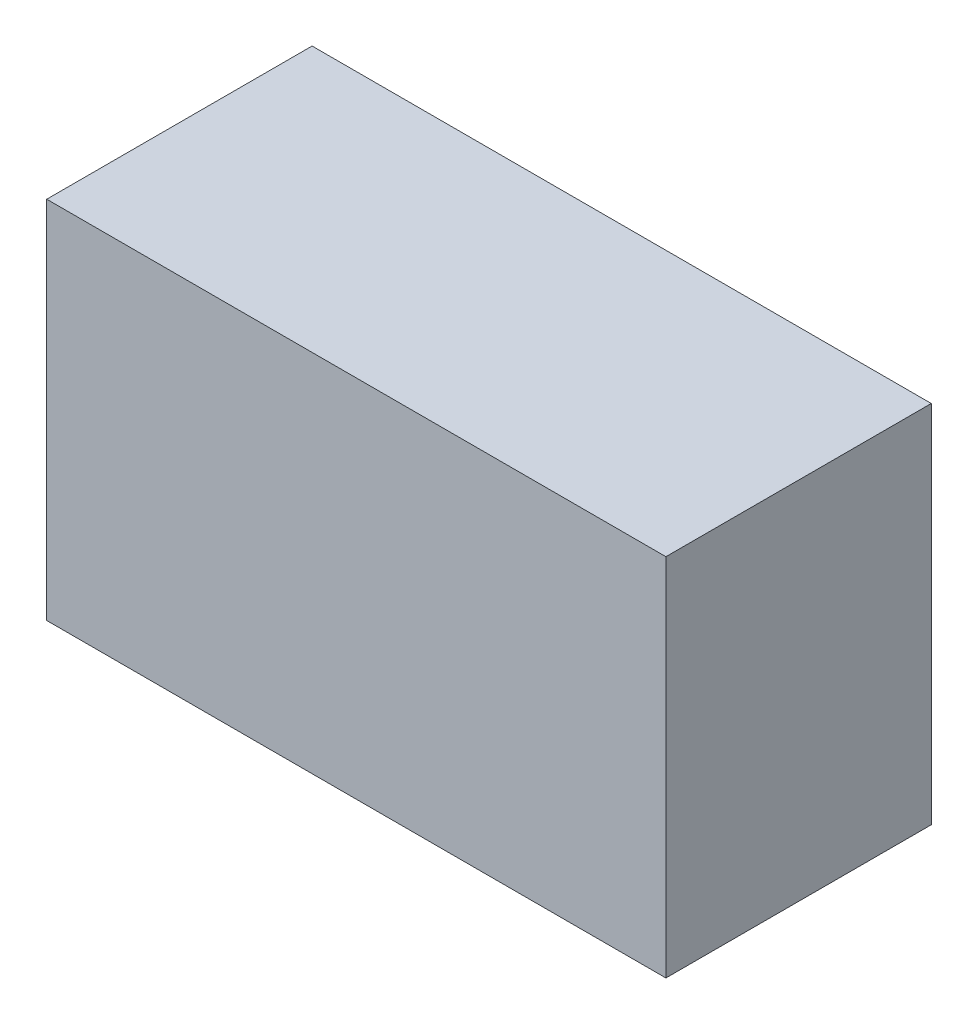
SolidWorks part; units mm, degrees
ref_plane "Front Plane" through (0, 0, 0) normal (0, 0, 1) x (1, 0, 0)
ref_plane "Top Plane" through (0, 0, 0) normal (0, 1, 0) x (1, 0, 0)
ref_plane "Right Plane" through (0, 0, 0) normal (1, 0, 0) x (0, 0, -1)
sketch "Sketch1" plane through (0, 0, 0) normal (0, 0, 1) x (1, 0, 0)
  line L0 (-355.6, 209.55) -> (355.6, -209.55) construction
  line L1 (-355.6, 209.55) -> (355.6, 209.55)
  line L2 (-355.6, 209.55) -> (-355.6, -209.55)
  line L3 (-355.6, -209.55) -> (355.6, -209.55)
  line L4 (355.6, 209.55) -> (355.6, -209.55)
  dimension "D1" = 711.2
  dimension "D2" = 419.1
extrude "Boss-Extrude1" add sketch "Sketch1" along normal mid plane 304.8
